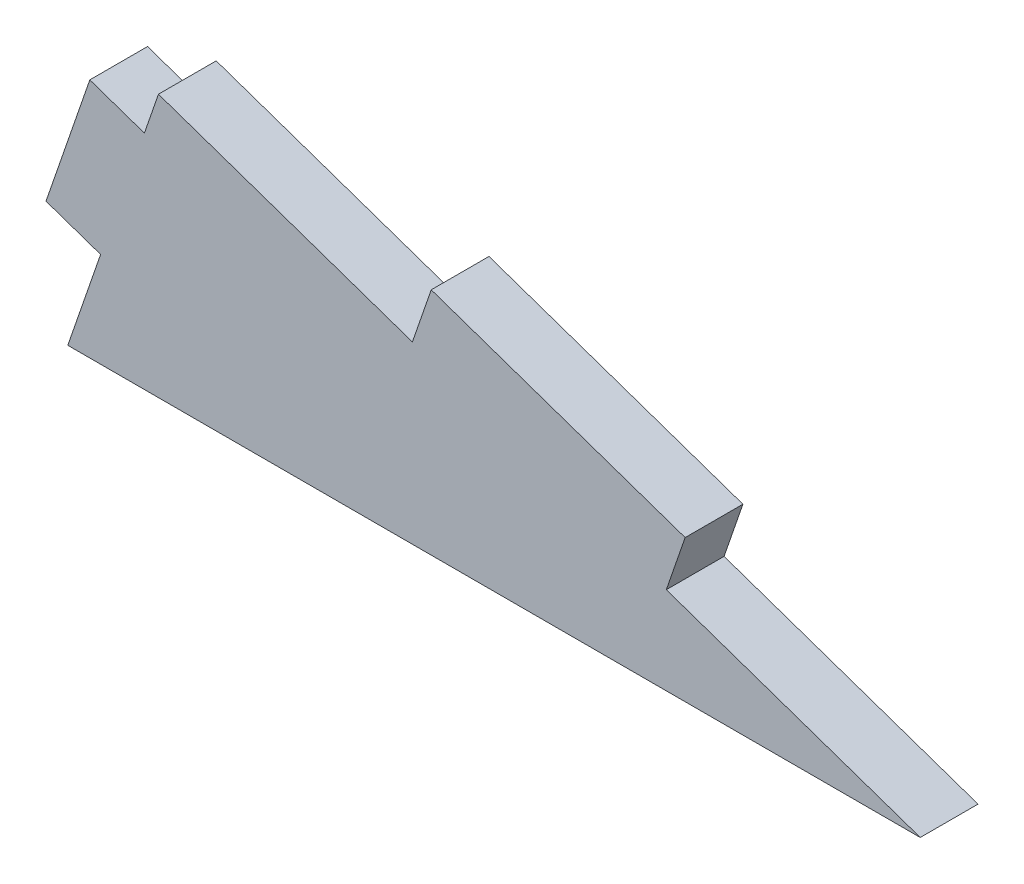
SolidWorks part; units mm, degrees
ref_plane "Front Plane" through (0, 0, 0) normal (0, 0, 1) x (1, 0, 0)
ref_plane "Top Plane" through (0, 0, 0) normal (0, 1, 0) x (1, 0, 0)
ref_plane "Right Plane" through (0, 0, 0) normal (1, 0, 0) x (0, 0, -1)
sketch "Sketch1" plane through (0, 0, 0) normal (0, 0, 1) x (1, 0, 0)
  line L0 (0, 0) -> (80.6074, 0)
  line L2 (80.6074, 0) -> (8.5738, 24.8516)
  line L3 (8.5738, 24.8516) -> (0, 0)
  point P1 (19.9369, 18.2832)
  point P3 (8.5735, 25.6564)
  point P6 (99.9689, 12.9149)
  point P7 (0, 0)
  point P8 (10.0404, 25.1187)
  dimension "D1" = 26.289
  dimension "D2" = 76.2
extrude "Boss-Extrude1" add sketch "Sketch1" along normal blind 5.461
sketch "Sketch2" plane through (0, 0, 5.461) normal (0, 0, 1) x (1, 0, 0)
  line L0 (8.5738, 24.8516) -> (0, 0) construction
  line L1 (7.2442, 20.9978) -> (2.0818, 22.7788)
  line L2 (7.2442, 20.9978) -> (3.1023, 8.9922)
  line L3 (3.1023, 8.9922) -> (-2.0601, 10.7732)
  line L4 (2.0818, 22.7788) -> (-2.0601, 10.7732)
  line L5 (80.6074, 0) -> (8.5738, 24.8516) construction
  line L6 (32.585, 16.5677) -> (56.5962, 8.2839)
  line L7 (32.585, 16.5677) -> (34.366, 21.7301)
  line L8 (56.5962, 8.2839) -> (58.3772, 13.4463)
  line L9 (34.366, 21.7301) -> (58.3772, 13.4463)
  point P6 (0, 0)
  point P7 (0, 0)
  point P8 (32.7628, 17.0742)
  point P15 (-2.7296, 5.9454)
  point P16 (3.8903, 19.0581)
  point P17 (0, 0)
  point P18 (54.2146, 9.4588)
  point P19 (44.5906, 12.4258)
  point P20 (4.663, 21.8883)
  dimension "D1" = 4.0767
  dimension "D2" = 5.461
  dimension "D3" = 12.7
  dimension "D4" = 25.4
  dimension "D5" = 5.461
extrude "Boss-Extrude2" add sketch "Sketch2" against normal up to surface (5.461 mm away) up to face at (29.7271, 8.2839, 0)
